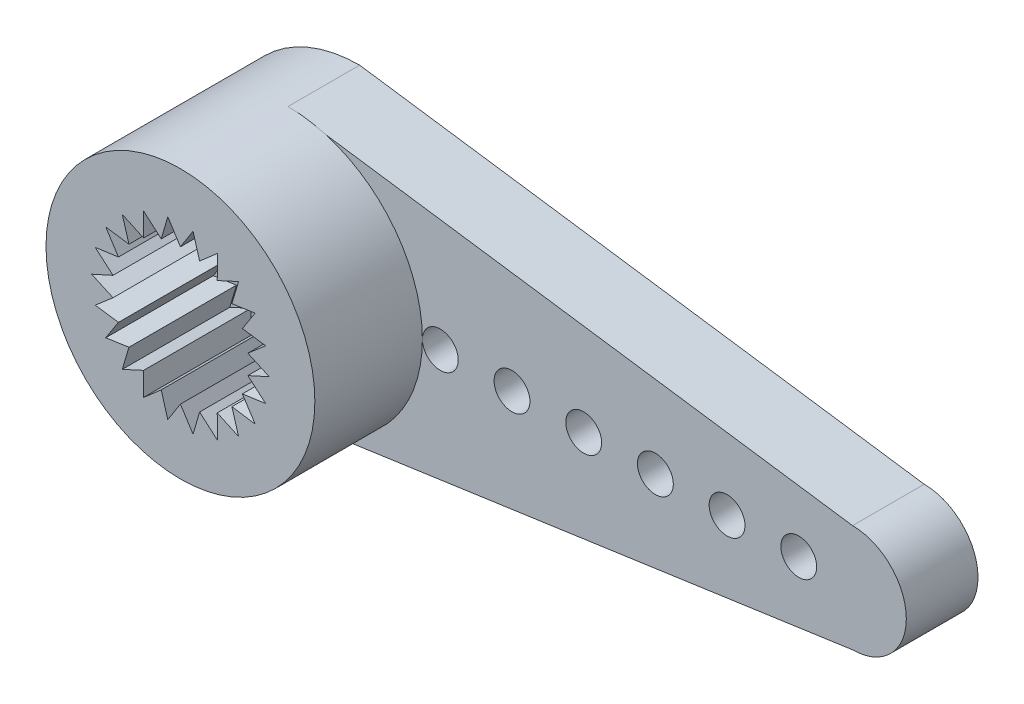
SolidWorks part; units mm, degrees
ref_plane "前视基准面" through (0, 0, 0) normal (0, 0, 1) x (1, 0, 0)
ref_plane "上视基准面" through (0, 0, 0) normal (0, 1, 0) x (1, 0, 0)
ref_plane "右视基准面" through (0, 0, 0) normal (1, 0, 0) x (0, 0, -1)
sketch "草图1" plane through (0, 0, 0) normal (0, 0, 1) x (1, 0, 0)
  line L1 (0, 3.75) -> (15.75, 1.5)
  line L2 (15.75, -1.5) -> (0, -3.75)
  arc A0 (0, 3.75) -> (0, -3.75) centre (0, 0) ccw
  circle A2 centre (14.25, 0) radius 0.5
  circle A3 centre (12.25, 0) radius 0.5
  circle A4 centre (10.25, 0) radius 0.5
  circle A5 centre (8.25, 0) radius 0.5
  circle A6 centre (6.25, 0) radius 0.5
  circle A7 centre (4.25, 0) radius 0.5
  arc A8 (15.75, -1.5) -> (15.75, 1.5) centre (15.75, 0) ccw
  dimension "D2" = 6
extrude "凸台-拉伸1" add sketch "草图1" along normal blind 2
sketch "草图2" plane through (0, 0, 0) normal (0, 0, -1) x (-1, 0, 0)
  circle A0 centre (0, 0) radius 2.5
extrude "切除-拉伸1" cut sketch "草图2" against normal blind 1.5
sketch "草图3" plane through (0, 0, 2) normal (0, 0, 1) x (1, 0, 0)
  circle A0 centre (0, 0) radius 3.75
extrude "凸台-拉伸2" add sketch "草图3" along normal blind 3
sketch "草图4" plane through (0, 0, 1.5) normal (0, 0, -1) x (-1, 0, 0)
  circle A0 centre (0, 0) radius 1.3
extrude "切除-拉伸2" cut sketch "草图4" against normal blind 9
sketch "草图5" plane through (0, 0, 5) normal (0, 0, 1) x (1, 0, 0)
  line L2 (0.45, -2.644) -> (-0.45, -2.644)
  line L3 (0, -1.939) -> (-0.45, -2.644)
  line L4 (-0.5353, -1.8621) -> (-1.1657, -2.4117)
  line L5 (-0.3021, -2.6653) -> (-1.1657, -2.4117)
  line L6 (-0.5353, -1.8621) -> (-0.3021, -2.6653)
  line L7 (-1.0272, -1.6374) -> (-1.7869, -1.9872)
  line L8 (-1.0298, -2.4738) -> (-1.7869, -1.9872)
  line L9 (-1.0272, -1.6374) -> (-1.0298, -2.4738)
  line L10 (-1.4359, -1.2833) -> (-2.2634, -1.4048)
  line L11 (-1.674, -2.085) -> (-2.2634, -1.4048)
  line L12 (-1.4359, -1.2833) -> (-1.674, -2.085)
  line L13 (-1.7283, -0.8283) -> (-2.5565, -0.7118)
  line L14 (-2.1826, -1.5305) -> (-2.5565, -0.7118)
  line L15 (-1.7283, -0.8283) -> (-2.1826, -1.5305)
  line L16 (-1.8807, -0.3094) -> (-2.6425, 0.0357)
  line L17 (-2.5144, -0.8552) -> (-2.6425, 0.0357)
  line L18 (-1.8807, -0.3094) -> (-2.5144, -0.8552)
  line L19 (-1.8807, 0.2314) -> (-2.5144, 0.7771)
  line L20 (-2.6425, -0.1137) -> (-2.5144, 0.7771)
  line L21 (-1.8807, 0.2314) -> (-2.6425, -0.1137)
  line L22 (-1.7283, 0.7503) -> (-2.1826, 1.4524)
  line L23 (-2.5565, 0.6338) -> (-2.1826, 1.4524)
  line L24 (-1.7283, 0.7503) -> (-2.5565, 0.6338)
  line L25 (-1.4359, 1.2052) -> (-1.674, 2.007)
  line L26 (-2.2634, 1.3268) -> (-1.674, 2.007)
  line L27 (-1.4359, 1.2052) -> (-2.2634, 1.3268)
  line L28 (-1.0272, 1.5594) -> (-1.0298, 2.3957)
  line L29 (-1.7869, 1.9091) -> (-1.0298, 2.3957)
  line L30 (-1.0272, 1.5594) -> (-1.7869, 1.9091)
  line L31 (-0.5353, 1.784) -> (-0.3021, 2.5872)
  line L32 (-1.1657, 2.3336) -> (-0.3021, 2.5872)
  line L33 (-0.5353, 1.784) -> (-1.1657, 2.3336)
  line L34 (0, 1.861) -> (0.45, 2.5659)
  line L35 (-0.45, 2.5659) -> (0.45, 2.5659)
  line L36 (0, 1.861) -> (-0.45, 2.5659)
  line L37 (0.5353, 1.784) -> (1.1657, 2.3336)
  line L38 (0.3021, 2.5872) -> (1.1657, 2.3336)
  line L39 (0.5353, 1.784) -> (0.3021, 2.5872)
  line L40 (1.0272, 1.5594) -> (1.7869, 1.9091)
  line L41 (1.0298, 2.3957) -> (1.7869, 1.9091)
  line L42 (1.0272, 1.5594) -> (1.0298, 2.3957)
  line L43 (1.4359, 1.2052) -> (2.2634, 1.3268)
  line L44 (1.674, 2.007) -> (2.2634, 1.3268)
  line L45 (1.4359, 1.2052) -> (1.674, 2.007)
  line L46 (1.7283, 0.7503) -> (2.5565, 0.6338)
  line L47 (2.1826, 1.4524) -> (2.5565, 0.6338)
  line L48 (1.7283, 0.7503) -> (2.1826, 1.4524)
  line L49 (1.8807, 0.2314) -> (2.6425, -0.1137)
  line L50 (2.5144, 0.7771) -> (2.6425, -0.1137)
  line L51 (1.8807, 0.2314) -> (2.5144, 0.7771)
  line L52 (1.8807, -0.3094) -> (2.5144, -0.8552)
  line L53 (2.6425, 0.0357) -> (2.5144, -0.8552)
  line L54 (1.8807, -0.3094) -> (2.6425, 0.0357)
  line L55 (1.7283, -0.8283) -> (2.1826, -1.5305)
  line L56 (2.5565, -0.7118) -> (2.1826, -1.5305)
  line L57 (1.7283, -0.8283) -> (2.5565, -0.7118)
  line L58 (1.4359, -1.2833) -> (1.674, -2.085)
  line L59 (2.2634, -1.4048) -> (1.674, -2.085)
  line L60 (1.4359, -1.2833) -> (2.2634, -1.4048)
  line L61 (1.0272, -1.6374) -> (1.0298, -2.4738)
  line L62 (1.7869, -1.9872) -> (1.0298, -2.4738)
  line L63 (1.0272, -1.6374) -> (1.7869, -1.9872)
  line L64 (0.5353, -1.8621) -> (0.3021, -2.6653)
  line L65 (1.1657, -2.4117) -> (0.3021, -2.6653)
  line L66 (0.5353, -1.8621) -> (1.1657, -2.4117)
  line L67 (0, -0.039) -> (0, -1.939) construction
  line L76 (-0.45, -2.644) -> (0, -2.644)
  line L78 (0, -1.939) -> (0.45, -2.644)
  dimension "D2" = 22
  dimension "D3" = 1.9
extrude "切除-拉伸4" cut sketch "草图5" against normal blind 3
